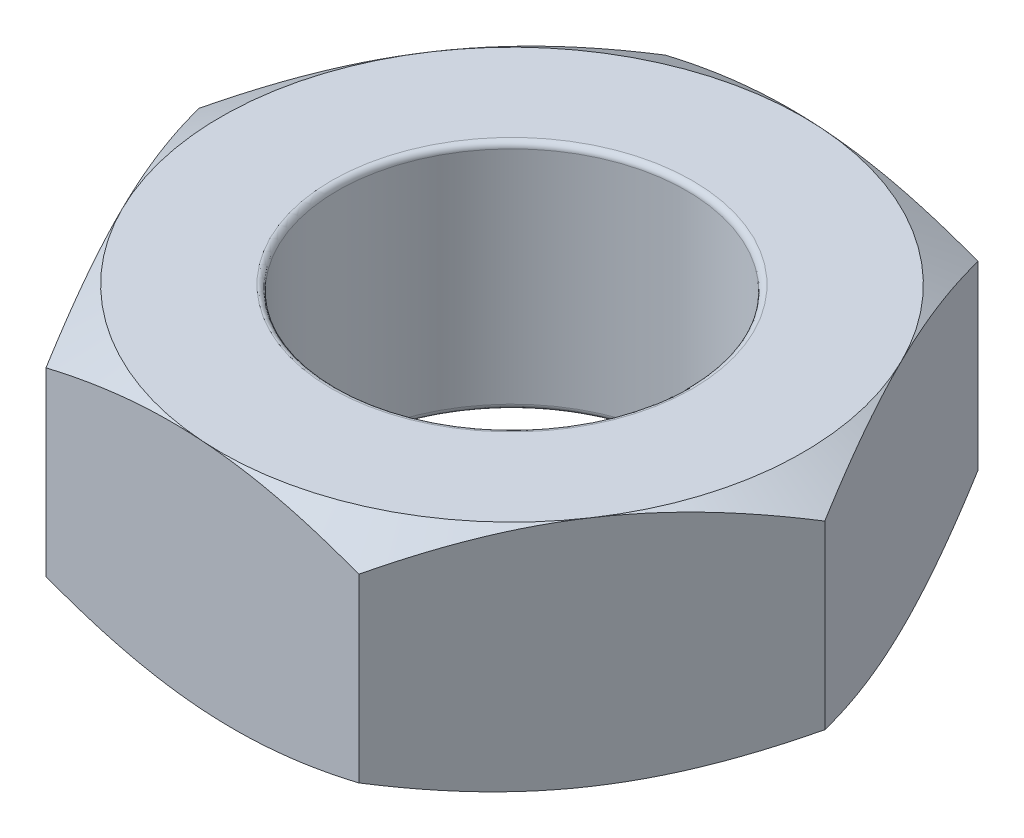
SolidWorks part; units mm, degrees
ref_plane "Front Plane" through (0, 0, 0) normal (0, 0, 1) x (1, 0, 0)
ref_plane "Top Plane" through (0, 0, 0) normal (0, 1, 0) x (1, 0, 0)
ref_plane "Right Plane" through (0, 0, 0) normal (1, 0, 0) x (0, 0, -1)
sketch "Sketch1" plane through (0, 0, 0) normal (0, 1, 0) x (1, 0, 0)
  line L1 (-2.8803, 0.1923) -> (-1.6067, -2.3983)
  line L2 (-1.6067, -2.3983) -> (1.2736, -2.5906)
  line L3 (1.2736, -2.5906) -> (2.8803, -0.1923)
  line L4 (2.8803, -0.1923) -> (1.6067, 2.3983)
  line L5 (1.6067, 2.3983) -> (-1.2736, 2.5906)
  line L6 (-1.2736, 2.5906) -> (-2.8803, 0.1923)
  circle A0 centre (0, 0) radius 2.5 construction
  circle A1 centre (0, 0) radius 1.5
  dimension "D1" = 5
  dimension "D2" = 3
extrude "Boss-Extrude1" add sketch "Sketch1" along normal blind 2
sketch "Sketch2" plane through (0, 2, 0) normal (0, 1, 0) x (1, 0, 0)
  circle A0 centre (0, 0) radius 2.5 construction
  circle A1 centre (0, 0) radius 2.5
extrude "Cut-Extrude1" cut sketch "Sketch2" against normal blind 2 draft 60 flip side to cut
sketch "Sketch3" plane through (0, 0, 0) normal (0, -1, 0) x (1, 0, 0)
  circle A0 centre (0, 0) radius 2.5 construction
  circle A1 centre (0, 0) radius 2.5
extrude "Cut-Extrude2" cut sketch "Sketch3" against normal blind 2 draft 60 flip side to cut
fillet "Fillet1" radius 0.05 2 edges at (0, 0, 1.5) (0, 2, 1.5)
